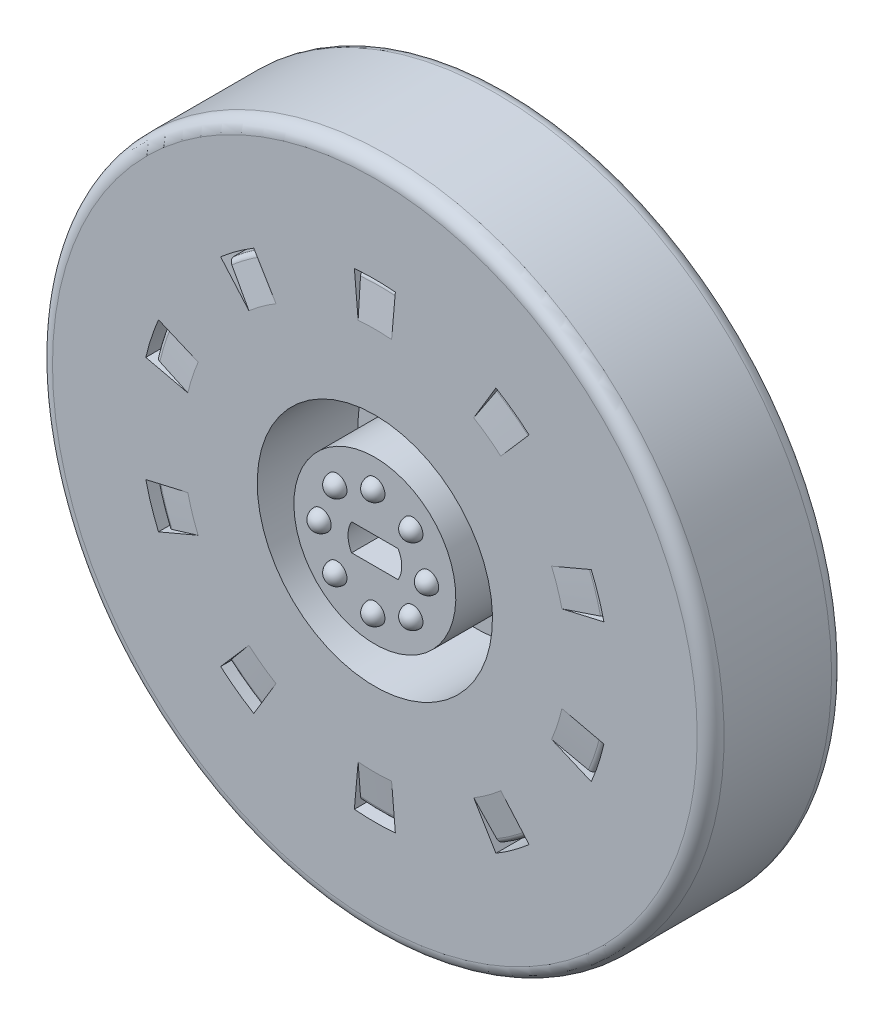
SolidWorks part; units mm, degrees
ref_plane "Front Plane" through (0, 0, 0) normal (0, 0, 1) x (1, 0, 0)
ref_plane "Top Plane" through (0, 0, 0) normal (0, 1, 0) x (1, 0, 0)
ref_plane "Right Plane" through (0, 0, 0) normal (1, 0, 0) x (0, 0, -1)
sketch "Sketch1" plane through (0, 0, 0) normal (1, 0, 0) x (0, 0, -1)
  line L0 (0, 0) -> (0, 12.0547)
  line L1 (0, 12.0547) -> (15, 12.0547)
  line L2 (15, 12.0547) -> (15, 17.5144)
  line L3 (15, 17.5144) -> (0, 17.5144)
  line L4 (0, 17.5144) -> (0, 50)
  line L5 (0, 50) -> (20, 50)
  line L6 (20, 50) -> (20, 40)
  line L7 (20, 40) -> (4.704, 40)
  line L8 (4.704, 40) -> (4.704, 30)
  line L9 (4.704, 30) -> (20, 30)
  line L10 (20, 30) -> (20, 0)
  line L11 (20, 0) -> (0, 0)
  dimension "D2" = 30
  dimension "D3" = 10
  dimension "D4" = 20
  dimension "D5" = 10
revolve "Revolve1" add sketch "Sketch1" angle 360 about L11
sketch "Sketch2" plane through (0, 0, 0) normal (1, 0, 0) x (0, 0, -1)
  line L0 (0, 28.58) -> (0.7973, 33.6738)
  line L2 (0, 50) -> (0, -50) construction
  line L4 (1.4645, 34.3406) -> (18.6496, 34.3406)
  line L5 (20, 28.58) -> (19.2483, 33.6808)
  line L6 (20, -50) -> (20, 50) construction
  line L8 (0, 0) -> (47.2496, 0) construction
  line L9 (0, 28.58) -> (0, 35)
  line L10 (0, 35) -> (20, 35)
  line L11 (20, 35) -> (20, 28.58)
  arc A0 (0.7973, 33.6738) -> (1.4645, 34.3406) centre (1.5877, 33.5501) cw
  arc A1 (19.2483, 33.6808) -> (18.6496, 34.3406) centre (18.4568, 33.5641) ccw
  dimension "D1" = 0.8
  dimension "D2" = 0.8
fillet "Fillet2" radius 2 2 edges at (0, 50, -20) (0, 50, 0)
sketch "Sketch3" plane through (0, 0, 0) normal (0, 0, 1) x (1, 0, 0)
  line L0 (-4, 0) -> (4, 0) construction
  line L1 (-3.4641, -2) -> (3.4641, -2)
  line L2 (-3.4641, 2) -> (3.4641, 2)
  line L3 (-4, -2) -> (4, -2) construction
  line L4 (-4, 2) -> (4, 2) construction
  arc A0 (-3.4641, 2) -> (-3.4641, -2) centre (0, 0) ccw
  arc A1 (3.4641, -2) -> (3.4641, 2) centre (0, 0) ccw
  dimension "D1" = 8
  dimension "D2" = 2
  dimension "D3" = 2
extrude "Cut-Extrude1" cut sketch "Sketch3" against normal blind 35
revolve "Cut-Revolve3" cut sketch "Sketch2" angle 10 mid plane about L8
pattern_circular "CirPattern6" count 10 over 360 about axis through (0, 0, 0) along (0, 0, 1) of "Cut-Revolve3"
sketch "Sketch4" plane through (0, 0, 0) normal (0, 0, 1) x (1, 0, 0)
  line L0 (-1.5, 8) -> (1.5, 8)
  arc A0 (1.5, 8) -> (-1.5, 8) centre (0, 8) ccw
  dimension "D1" = 1.5
  dimension "D2" = 8
sketch "Sketch6" plane through (0, 0, -20) normal (0, 0, -1) x (-1, 0, 0)
  circle A0 centre (0, 0) radius 16.7971
extrude "Boss-Extrude2" add sketch "Sketch6" along normal blind 10
revolve "Revolve4" add sketch "Sketch4" angle 360 about L0
pattern_circular "CirPattern5" count 8 over 360 about axis through (0, 0, 0) along (0, 0, 1) of "Revolve4"
sketch "Sketch9" plane through (0, 0, -30) normal (0, 0, -1) x (-1, 0, 0)
  circle A0 centre (0, 0) radius 4
extrude "Cut-Extrude4" cut sketch "Sketch9" against normal up to surface (10 mm away) up to face at (0, 0, -20)
